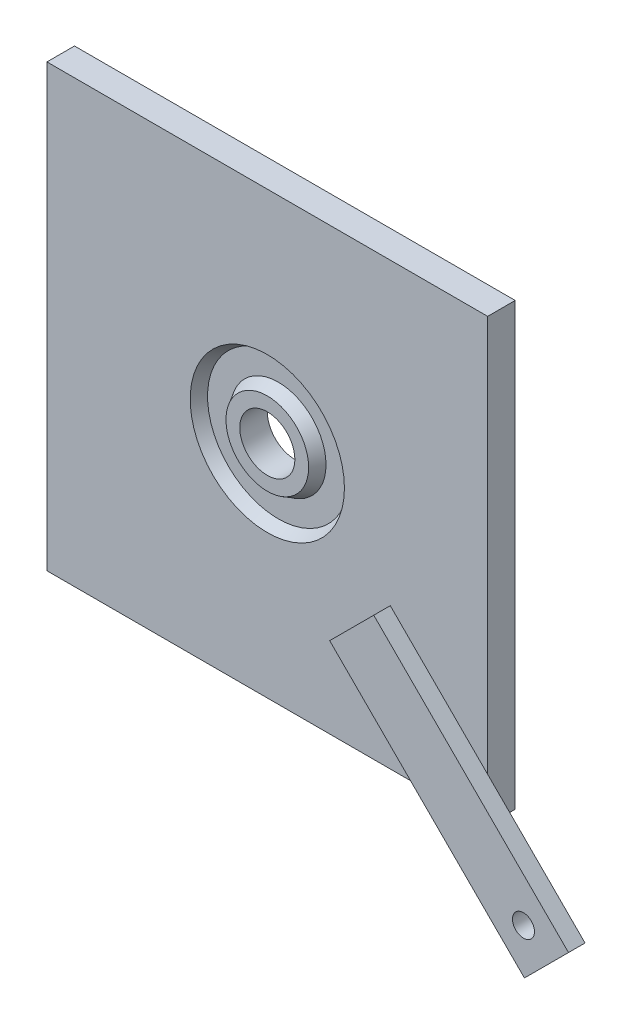
SolidWorks part; units mm, degrees
material "7075-O (SS)"
ref_plane "Front Plane" through (0, 0, 0) normal (0, 0, 1) x (1, 0, 0)
ref_plane "Top Plane" through (0, 0, 0) normal (0, 1, 0) x (1, 0, 0)
ref_plane "Right Plane" through (0, 0, 0) normal (1, 0, 0) x (0, 0, -1)
sketch "Sketch1" plane through (0, 0, 0) normal (0, 0, 1) x (1, 0, 0)
  line L1 (-40, -40) -> (40, -40)
  line L2 (-40, -40) -> (-40, 40)
  line L3 (-40, 40) -> (40, 40)
  line L4 (40, -40) -> (40, 40)
  line L5 (-40, -40) -> (40, 40) construction
  line L6 (-40, 40) -> (40, -40) construction
  circle A0 centre (0, 0) radius 5
  point P0 (0, 0)
  dimension "D3" = 10
  dimension "D1" = 80
  dimension "D2" = 80
extrude "Boss-Extrude1" add sketch "Sketch1" along normal blind 5
sketch "Sketch2" plane through (0, 0, 5) normal (0, 0, 1) x (1, 0, 0)
  circle A0 centre (0, 0) radius 14
  circle A1 centre (0, 0) radius 7.5
  dimension "D1" = 28
  dimension "D2" = 15
extrude "Cut-Extrude1" cut sketch "Sketch2" against normal blind 2 draft 30
sketch "Sketch3" plane through (0, 0, 5) normal (0, 0, 1) x (1, 0, 0)
  line L0 (40, -40) -> (28.2095, -28.2095) construction
  line L1 (40, -40) -> (40, 40) construction
  line L2 (49.6777, -57.6777) -> (14.3223, -22.3223)
  line L5 (-40, -40) -> (40, -40) construction
  line L6 (57.6777, -49.6777) -> (22.3223, -14.3223)
  line L7 (14.3223, -22.3223) -> (22.3223, -14.3223)
  line L8 (49.6777, -57.6777) -> (57.6777, -49.6777)
  circle A0 centre (49.4975, -49.4975) radius 2
  point P8 (32, -40)
  dimension "D5" = 4
  dimension "D6" = 70
  dimension "D1" = 45
  dimension "D2" = 50
  dimension "D3" = 0
  dimension "D4" = 8
extrude "Boss-Extrude2" add sketch "Sketch3" along normal blind 3
